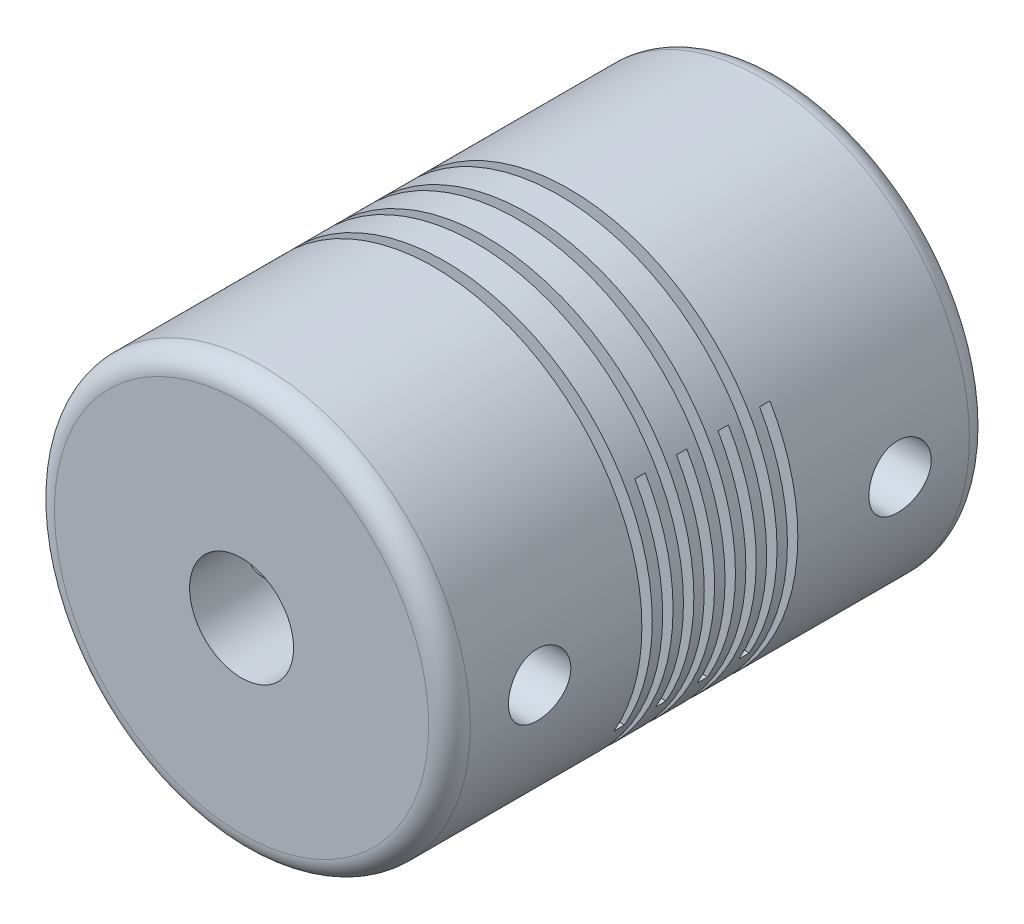
SolidWorks part; units mm, degrees
material "AISI 1020"
ref_plane "Спереди" through (0, 0, 0) normal (0, 0, 1) x (1, 0, 0)
ref_plane "Сверху" through (0, 0, 0) normal (0, 1, 0) x (1, 0, 0)
ref_plane "Справа" through (0, 0, 0) normal (1, 0, 0) x (0, 0, -1)
sketch "Эскиз1" plane through (0, 0, 0) normal (0, 0, 1) x (1, 0, 0)
  circle A0 centre (0, 0) radius 10
  circle A1 centre (0, 0) radius 2.5
  dimension "D1" = 20
  dimension "D2" = 5
extrude "Бобышка-Вытянуть1" add sketch "Эскиз1" against normal blind 26
sketch "Эскиз2" plane through (0, 0, 0) normal (1, 0, 0) x (0, 0, -1)
  line L0 (0, 0) -> (8.6667, 0) construction
  line L1 (8.6667, 0) -> (17.3333, 0) construction
  line L2 (17.3333, 0) -> (26, 0) construction
  line L3 (26, -10) -> (26, 10) construction
  line L4 (26, 10) -> (0, 10) construction
  line L5 (13.25, 10) -> (13.75, 10)
  line L6 (13.25, 10) -> (13.25, -5)
  line L7 (13.25, -5) -> (13.75, -5)
  line L8 (13.75, 10) -> (13.75, -5)
  line L9 (13, -1000) -> (13, 49000) construction
  line L10 (17.3333, 0) -> (17.3333, -10) construction
  line L11 (17.3333, 0) -> (17.3333, 10) construction
  line L12 (15.25, -5) -> (15.75, -5)
  line L13 (14.25, 5) -> (14.75, 5)
  line L14 (14.25, 5) -> (14.25, -10)
  line L15 (14.25, -10) -> (14.75, -10)
  line L16 (14.75, 5) -> (14.75, -10)
  line L17 (15.25, 10) -> (15.25, -5)
  line L18 (15.75, 10) -> (15.75, -5)
  line L19 (16.25, 5) -> (16.25, -10)
  line L20 (16.25, -10) -> (16.75, -10)
  line L21 (16.75, 5) -> (16.75, -10)
  line L22 (15.25, 10) -> (15.75, 10)
  line L23 (16.25, 5) -> (16.75, 5)
  line L24 (10.6667, 0) -> (19.3333, 0) construction
  line L25 (11.25, 10) -> (11.25, -5)
  line L26 (11.25, 10) -> (11.75, 10)
  line L27 (11.75, 10) -> (11.75, -5)
  line L28 (11.25, -5) -> (11.75, -5)
  line L29 (12.25, 5) -> (12.25, -10)
  line L30 (12.25, 5) -> (12.75, 5)
  line L31 (12.75, 5) -> (12.75, -10)
  line L32 (12.25, -10) -> (12.75, -10)
  line L33 (9.25, 10) -> (9.25, -5)
  line L34 (9.25, 10) -> (9.75, 10)
  line L35 (9.75, 10) -> (9.75, -5)
  line L36 (9.25, -5) -> (9.75, -5)
  line L37 (10.25, 5) -> (10.25, -10)
  line L38 (10.25, 5) -> (10.75, 5)
  line L39 (10.75, 5) -> (10.75, -10)
  line L40 (10.25, -10) -> (10.75, -10)
  circle A0 centre (4.3333, 0) radius 1.5
  circle A1 centre (21.6667, 0) radius 1.5
  point P13 (17.3333, -5)
  point P16 (17.3333, 5)
  point P18 (13, 0)
  point P19 (14.5, 5)
  dimension "D6" = 3
  dimension "D1" = 0.5
  dimension "D2" = 0.5
  dimension "D3" = 0.5
  dimension "D4" = 2
  dimension "D5" = 3
extrude "Вырез-Вытянуть1" cut sketch "Эскиз2" against normal through all both and the other way through all
sketch "Эскиз3" plane through (0, 0, -26) normal (0, 0, -1) x (-1, 0, 0)
  circle A0 centre (0, 0) radius 3
  dimension "D1" = 6
extrude "Вырез-Вытянуть2" cut sketch "Эскиз3" against normal up to surface (9.25 mm away) up to face at (0, -2.5, -16.75)
fillet "Скругление1" radius 1 2 edges at (10, 0, 0) (10, 0, -26)
equation "\"D2@Эскиз2\"=\"D1@Эскиз2\""
equation "\"D3@Эскиз2\"=\"D1@Эскиз2\""
